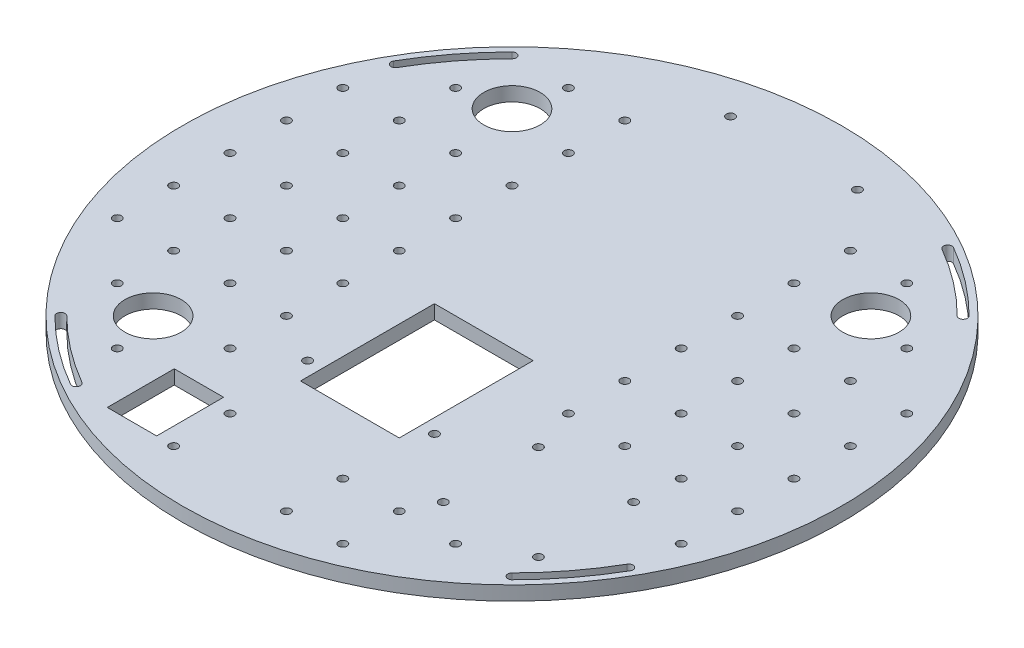
SolidWorks part; units mm, degrees
ref_plane "Front Plane" through (0, 0, 0) normal (0, 0, 1) x (1, 0, 0)
ref_plane "Top Plane" through (0, 0, 0) normal (0, 1, 0) x (1, 0, 0)
ref_plane "Right Plane" through (0, 0, 0) normal (1, 0, 0) x (0, 0, -1)
sketch "Sketch18" plane through (0, 0, 0) normal (0, 1, 0) x (1, 0, 0)
  circle A0 centre (0, 0) radius 148.4312
  dimension "D1" = 296.8625
extrude "Boss-Extrude1" add sketch "Sketch18" along normal blind 6.35
sketch "Sketch19" plane through (0, 6.35, 0) normal (0, 1, 0) x (1, 0, 0)
  line L0 (-71.842, -124.4341) -> (-124.4341, 71.842)
  line L1 (-101.6, -101.6) -> (101.6, -101.6)
  line L2 (-101.6, -101.6) -> (-101.6, 101.6)
  line L3 (-101.6, 101.6) -> (101.6, 101.6)
  line L4 (101.6, -101.6) -> (101.6, 101.6)
  line L5 (-101.6, -101.6) -> (101.6, 101.6) construction
  line L6 (-101.6, 101.6) -> (101.6, -101.6) construction
  line L7 (-71.842, -124.4341) -> (124.4341, -71.842)
  line L8 (124.4341, -71.842) -> (71.842, 124.4341)
  line L9 (-124.4341, 71.842) -> (71.842, 124.4341)
  line L18 (-86.7516, 29.347) -> (60.4555, 68.791)
  line L19 (-76.2, -50.8) -> (76.2, -50.8)
  line L20 (-76.2, -50.8) -> (-76.2, 50.8)
  line L21 (-76.2, 50.8) -> (76.2, 50.8)
  line L22 (76.2, -50.8) -> (76.2, 50.8)
  line L23 (-76.2, -50.8) -> (76.2, 50.8) construction
  line L24 (-76.2, 50.8) -> (76.2, -50.8) construction
  line L25 (-60.4555, -68.791) -> (-86.7516, 29.347)
  line L26 (-60.4555, -68.791) -> (86.7516, -29.347)
  line L27 (86.7516, -29.347) -> (60.4555, 68.791)
  circle A0 centre (0, 0) radius 143.6841
  point P0 (0, 0)
  dimension "D1" = 203.2
  dimension "D3" = 15
  dimension "D4" = 152.4
  dimension "D5" = 101.6
  dimension "D2" = 2
  dimension "D6" = 2
hole_wizard "#6 Clearance Hole1" positions "Sketch20" profile "Sketch21" hole size "#6" standard "ANSI Inch" end condition through all
sketch "Sketch20" plane through (0, 6.35, 0) normal (0, 1, 0) x (1, 0, 0)
  point P0 (-101.6, 101.6)
  point P3 (101.6, 101.6)
  point P6 (101.6, -101.6)
  point P9 (-101.6, -101.6)
  point P13 (-124.4341, 71.842)
  point P16 (-71.842, -124.4341)
  point P19 (124.4341, -71.842)
  point P22 (71.842, 124.4341)
  point P51 (0, 0)
  point P52 (0, 0)
  point P53 (0, 0)
sketch "Sketch21" plane through (-101.6, 6.35, -101.6) normal (1, 0, 0) x (0, 0, 1)
  line L0 (0, 0) -> (0, 6.35)
  line L1 (0, 6.35) -> (1.8986, 6.35)
  line L2 (1.8986, 6.35) -> (1.8986, 0)
  line L5 (1.8986, 0) -> (0, 0)
  line L11 (0, -6.35) -> (0, 107.95) construction
  dimension "Thru Hole Dia." = 3.7973
  dimension "Thru Hole Depth" = 6.35
sketch "Sketch23" plane through (0, 6.35, 0) normal (0, 1, 0) x (1, 0, 0)
  circle A0 centre (124.4341, -71.842) radius 1.8987 construction
  circle A1 centre (101.6, -101.6) radius 1.8986 construction
  circle A2 centre (-71.842, -124.4341) radius 1.8986 construction
  circle A3 centre (-101.6, -101.6) radius 1.8986 construction
  circle A4 centre (101.6, 101.6) radius 1.8986 construction
  circle A5 centre (71.842, 124.4341) radius 1.8986 construction
  circle A6 centre (-101.6, 101.6) radius 1.8986 construction
  circle A7 centre (-124.4341, 71.842) radius 1.8986 construction
  circle A8 centre (124.4341, -71.842) radius 1.8987
  circle A9 centre (101.6, -101.6) radius 1.8986
  circle A10 centre (-71.842, -124.4341) radius 1.8986
  circle A11 centre (-101.6, -101.6) radius 1.8986
  circle A12 centre (101.6, 101.6) radius 1.8986
  circle A13 centre (71.842, 124.4341) radius 1.8986
  circle A14 centre (-101.6, 101.6) radius 1.8986
  circle A15 centre (-124.4341, 71.842) radius 1.8986
  arc A16 (-124.4341, 71.842) -> (-101.6, 101.6) centre (0, 0) cw construction
  arc A17 (-102.9425, 102.9425) -> (-126.0784, 72.7914) centre (0, 0) ccw
  arc A18 (-100.2575, 100.2575) -> (-122.7898, 70.8927) centre (0, 0) ccw
  arc A19 (-100.2575, 100.2575) -> (-102.9425, 102.9425) centre (-101.6, 101.6) ccw
  arc A20 (-126.0784, 72.7914) -> (-122.7898, 70.8927) centre (-124.4341, 71.842) ccw
  arc A21 (71.842, 124.4341) -> (101.6, 101.6) centre (0, 0) cw construction
  arc A22 (102.9425, 102.9425) -> (72.7914, 126.0784) centre (0, 0) ccw
  arc A23 (100.2575, 100.2575) -> (70.8927, 122.7898) centre (0, 0) ccw
  arc A24 (100.2575, 100.2575) -> (102.9425, 102.9425) centre (101.6, 101.6) ccw
  arc A25 (72.7914, 126.0784) -> (70.8927, 122.7898) centre (71.842, 124.4341) ccw
  arc A26 (101.6, -101.6) -> (124.4341, -71.842) centre (0, 0) ccw construction
  arc A27 (102.9425, -102.9425) -> (126.0784, -72.7914) centre (0, 0) ccw
  arc A28 (100.2575, -100.2575) -> (122.7898, -70.8927) centre (0, 0) ccw
  arc A29 (100.2575, -100.2575) -> (102.9425, -102.9425) centre (101.6, -101.6) ccw
  arc A30 (126.0784, -72.7914) -> (122.7898, -70.8927) centre (124.4341, -71.842) ccw
  arc A31 (-101.6, -101.6) -> (-71.842, -124.4341) centre (0, 0) ccw construction
  arc A32 (-102.9425, -102.9425) -> (-72.7914, -126.0784) centre (0, 0) ccw
  arc A33 (-100.2575, -100.2575) -> (-70.8927, -122.7898) centre (0, 0) ccw
  arc A34 (-100.2575, -100.2575) -> (-102.9425, -102.9425) centre (-101.6, -101.6) ccw
  arc A35 (-72.7914, -126.0784) -> (-70.8927, -122.7898) centre (-71.842, -124.4341) ccw
  point P27 (-113.9923, 87.4693)
  point P35 (87.4693, 113.9923)
  point P43 (113.9923, -87.4693)
  point P50 (-87.4693, -113.9923)
  point P55 (0, 0)
  circle M9 centre (-124.4341, 71.842) radius 1.8986
  circle M10 centre (-71.842, -124.4341) radius 1.8986
  circle M11 centre (124.4341, -71.842) radius 1.8987
  circle M12 centre (71.842, 124.4341) radius 1.8986
extrude "Cut-Extrude1" cut sketch "Sketch23" against normal blind 6.35 contours A33 A11 A32 M10 | A18 A14 A17 M9 | A23 A12 A22 M12 | A28 A9 A27 M11
sketch "Sketch24" plane through (0, 6.35, 0) normal (0, 1, 0) x (1, 0, 0)
  line L1 (-28.575, -63.5) -> (28.575, -63.5)
  line L2 (-28.575, -63.5) -> (-28.575, 127)
  line L3 (-28.575, 127) -> (28.575, 127)
  line L4 (28.575, -63.5) -> (28.575, 127)
  line L5 (-28.575, -63.5) -> (28.575, 127) construction
  line L6 (-28.575, 127) -> (28.575, -63.5) construction
  line L7 (57.15, -88.1063) -> (100.0125, -88.1063)
  line L8 (57.15, -88.1063) -> (57.15, -45.2437)
  line L9 (57.15, -45.2437) -> (100.0125, -45.2437)
  line L10 (100.0125, -88.1063) -> (100.0125, -45.2437)
  line L11 (57.15, -88.1063) -> (100.0125, -45.2437) construction
  line L12 (57.15, -45.2437) -> (100.0125, -88.1063) construction
  circle A0 centre (0, 0) radius 148.4312 construction
  point P0 (0, 31.75)
  point P5 (81.9016, -82.55)
  point P6 (0, 0)
  point P10 (78.5813, -66.675)
  dimension "D1" = 190.5
  dimension "D2" = 57.15
  dimension "D3" = 127
  dimension "D4" = 42.8625
  dimension "D5" = 28.575
  dimension "D6" = 3.175
hole_wizard "#6 Clearance Hole2" positions "Sketch25" profile "Sketch26" hole size "#6" standard "ANSI Inch" end condition through all
sketch "Sketch25" plane through (0, 6.35, 0) normal (0, 1, 0) x (1, 0, 0)
  point P0 (57.15, -45.2437)
  point P3 (57.15, -88.1063)
  point P6 (100.0125, -88.1063)
  point P9 (100.0125, -45.2437)
  point P12 (-28.575, -63.5)
  point P15 (28.575, -63.5)
  point P18 (-28.575, 127)
  point P21 (28.575, 127)
sketch "Sketch26" plane through (57.15, 6.35, 45.2437) normal (1, 0, 0) x (0, 0, 1)
  line L0 (0, 0) -> (0, 6.35)
  line L1 (0, 6.35) -> (1.8986, 6.35)
  line L2 (1.8986, 6.35) -> (1.8986, 0)
  line L5 (1.8986, 0) -> (0, 0)
  line L11 (0, -6.35) -> (0, 107.95) construction
  dimension "Thru Hole Dia." = 3.7973
  dimension "Thru Hole Depth" = 6.35
sketch "Sketch29" plane through (0, 6.35, 0) normal (0, 1, 0) x (1, 0, 0)
  line L0 (-22.225, -73.025) -> (-22.225, -12.7)
  line L1 (-19.05, -69.85) -> (19.05, -69.85)
  line L2 (-19.05, -69.85) -> (-19.05, -15.875) construction
  line L3 (-19.05, -15.875) -> (19.05, -15.875)
  line L4 (19.05, -69.85) -> (19.05, -15.875)
  line L5 (-19.05, -69.85) -> (19.05, -15.875) construction
  line L6 (-19.05, -15.875) -> (19.05, -69.85) construction
  line L7 (-22.225, -12.7) -> (22.225, -12.7)
  line L8 (22.225, -73.025) -> (22.225, -12.7)
  line L9 (-22.225, -73.025) -> (22.225, -73.025)
  circle A1 centre (-28.575, -63.5) radius 1.8986 construction
  point P0 (0, -42.8625)
  point P5 (0, 94.9421)
  point P6 (0, 0)
  point P7 (0, -41.112)
  dimension "D3" = 6.35
  dimension "D1" = 38.1
  dimension "D2" = 53.975
  dimension "D4" = 3.175
extrude "Cut-Extrude2" cut sketch "Sketch29" against normal through all
sketch "Sketch30" plane through (0, 6.35, 0) normal (0, 1, 0) x (1, 0, 0)
  line L0 (-80.8223, 80.8223) -> (-80.8223, -80.8223) construction
  line L1 (-55.4223, -126.8598) -> (-33.1973, -126.8598)
  line L2 (-55.4223, -126.8598) -> (-55.4223, -96.6973)
  line L3 (-55.4223, -96.6973) -> (-33.1973, -96.6973)
  line L4 (-33.1973, -126.8598) -> (-33.1973, -96.6973)
  line L5 (-55.4223, -126.8598) -> (-33.1973, -96.6973) construction
  line L6 (-55.4223, -96.6973) -> (-33.1973, -126.8598) construction
  line L7 (-80.8223, 80.8223) -> (80.8223, 80.8223) construction
  circle A0 centre (-80.8223, 80.8223) radius 12.7
  circle A1 centre (80.8223, 80.8223) radius 12.7
  circle A2 centre (-80.8223, -80.8223) radius 12.7
  circle A3 centre (0, 0) radius 114.3 construction
  point P6 (-44.3098, -111.7786)
  point P14 (-130.789, 0)
  point P15 (0, 0)
  point P16 (0, 0)
  point P17 (-47.0634, -107.5133)
  dimension "D1" = 228.6
  dimension "D2" = 25.4
  dimension "D3" = 30.1625
  dimension "D4" = 22.225
  dimension "D5" = 25.4
  dimension "D6" = 15.875
extrude "Cut-Extrude3" cut sketch "Sketch30" against normal blind 6.35
sketch "Sketch31" plane through (0, 6.35, 0) normal (0, 1, 0) x (1, 0, 0)
  line L0 (-25.4, 0) -> (0, 0) construction
  line L1 (0, -148.4312) -> (0, 148.4312) construction
  circle A0 centre (0, 0) radius 148.4312 construction
  point P0 (-25.4, 0)
  point P3 (0, 0)
  point P5 (25.4, 127)
  point P6 (-50.8, 0)
  point P7 (-76.2, 0)
  point P8 (-101.6, 0)
  point P9 (-127, 0)
  point P10 (-50.8, 25.4)
  point P11 (-76.2, 25.4)
  point P12 (-101.6, 25.4)
  point P13 (-127, 25.4)
  point P14 (-50.8, 50.8)
  point P15 (-76.2, 50.8)
  point P16 (-101.6, 50.8)
  point P17 (-127, 50.8)
  point P18 (-50.8, 76.2)
  point P19 (-76.2, 76.2)
  point P20 (-101.6, 76.2)
  point P21 (-127, 76.2)
  point P22 (-50.8, 101.6)
  point P23 (-76.2, 101.6)
  point P24 (-101.6, 101.6)
  point P25 (-127, 101.6)
  point P26 (-50.8, 127)
  point P27 (-76.2, 127)
  point P28 (-101.6, 127)
  point P29 (-127, 127)
  point P30 (-25.4, 25.4)
  point P31 (-25.4, 50.8)
  point P32 (-25.4, 76.2)
  point P33 (-25.4, 101.6)
  point P34 (-25.4, 127)
  point P39 (25.4, 101.6)
  point P40 (25.4, 76.2)
  point P41 (25.4, 50.8)
  point P42 (25.4, 25.4)
  point P43 (127, 127)
  point P44 (101.6, 127)
  point P45 (76.2, 127)
  point P46 (50.8, 127)
  point P47 (127, 101.6)
  point P48 (101.6, 101.6)
  point P49 (76.2, 101.6)
  point P50 (50.8, 101.6)
  point P51 (127, 76.2)
  point P52 (101.6, 76.2)
  point P53 (76.2, 76.2)
  point P54 (50.8, 76.2)
  point P55 (127, 50.8)
  point P56 (101.6, 50.8)
  point P57 (76.2, 50.8)
  point P58 (50.8, 50.8)
  point P59 (127, 25.4)
  point P60 (101.6, 25.4)
  point P61 (76.2, 25.4)
  point P62 (50.8, 25.4)
  point P63 (127, 0)
  point P64 (101.6, 0)
  point P65 (76.2, 0)
  point P66 (50.8, 0)
  point P67 (25.4, 0)
  point P69 (50.8, -25.4)
  point P70 (76.2, -25.4)
  point P71 (101.6, -25.4)
  point P72 (127, -25.4)
  point P73 (50.8, -50.8)
  point P74 (76.2, -50.8)
  point P75 (101.6, -50.8)
  point P76 (127, -50.8)
  point P77 (50.8, -76.2)
  point P78 (76.2, -76.2)
  point P79 (101.6, -76.2)
  point P80 (127, -76.2)
  point P81 (50.8, -101.6)
  point P82 (76.2, -101.6)
  point P83 (101.6, -101.6)
  point P84 (127, -101.6)
  point P85 (50.8, -127)
  point P86 (76.2, -127)
  point P87 (101.6, -127)
  point P88 (127, -127)
  point P89 (25.4, -25.4)
  point P90 (25.4, -50.8)
  point P91 (25.4, -76.2)
  point P92 (25.4, -101.6)
  point P93 (-25.4, -127)
  point P94 (-25.4, -101.6)
  point P95 (-25.4, -76.2)
  point P96 (-25.4, -50.8)
  point P97 (-25.4, -25.4)
  point P98 (-127, -127)
  point P99 (-101.6, -127)
  point P100 (-76.2, -127)
  point P101 (-50.8, -127)
  point P102 (-127, -101.6)
  point P103 (-101.6, -101.6)
  point P104 (-76.2, -101.6)
  point P105 (-50.8, -101.6)
  point P106 (-127, -76.2)
  point P107 (-101.6, -76.2)
  point P108 (-76.2, -76.2)
  point P109 (-50.8, -76.2)
  point P110 (-127, -50.8)
  point P111 (-101.6, -50.8)
  point P112 (-76.2, -50.8)
  point P113 (-50.8, -50.8)
  point P114 (-127, -25.4)
  point P115 (-101.6, -25.4)
  point P116 (-76.2, -25.4)
  point P117 (-50.8, -25.4)
  point P118 (25.4, -127)
  dimension "D1" = 25.4
  dimension "D2" = 5
  dimension "D3" = 6
hole_wizard "#6 Clearance Hole3" positions "Sketch32" profile "Sketch33" hole size "#6" standard "ANSI Inch" end condition through all
sketch "Sketch32" plane through (0, 6.35, 0) normal (0, 1, 0) x (1, 0, 0)
  point P0 (-50.8, 101.6)
  point P3 (-76.2, 101.6)
  point P6 (-101.6, 76.2)
  point P9 (-50.8, 76.2)
  point P12 (-50.8, 50.8)
  point P15 (-76.2, 50.8)
  point P18 (-101.6, 50.8)
  point P21 (-127, 50.8)
  point P24 (-50.8, 25.4)
  point P27 (-76.2, 25.4)
  point P30 (-101.6, 25.4)
  point P33 (-127, 25.4)
  point P36 (-101.6, 0)
  point P39 (-127, 0)
  point P42 (-127, -25.4)
  point P45 (-101.6, -25.4)
  point P48 (-127, -50.8)
  point P51 (-101.6, -50.8)
  point P54 (-101.6, -76.2)
  point P57 (-76.2, -101.6)
  point P60 (-50.8, -76.2)
  point P63 (-76.2, -50.8)
  point P66 (-50.8, -50.8)
  point P69 (-50.8, -25.4)
  point P72 (-76.2, -25.4)
  point P75 (-76.2, 0)
  point P78 (-50.8, 0)
  point P81 (50.8, 101.6)
  point P84 (76.2, 101.6)
  point P87 (50.8, 76.2)
  point P90 (101.6, 76.2)
  point P93 (101.6, 50.8)
  point P96 (127, 50.8)
  point P99 (127, 25.4)
  point P102 (127, 0)
  point P105 (127, -25.4)
  point P108 (50.8, 50.8)
  point P111 (50.8, 25.4)
  point P114 (50.8, 0)
  point P117 (50.8, -25.4)
  point P120 (76.2, -25.4)
  point P123 (101.6, -25.4)
  point P126 (101.6, 0)
  point P129 (76.2, 0)
  point P132 (76.2, 25.4)
  point P135 (76.2, 50.8)
  point P138 (101.6, 25.4)
  point P141 (127, -50.8)
  point P144 (76.2, -101.6)
  point P147 (50.8, -101.6)
  point P150 (-25.4, -101.6)
  point P153 (25.4, -101.6)
  point P156 (25.4, -127)
  point P159 (50.8, -127)
  point P162 (-25.4, -127)
sketch "Sketch33" plane through (-50.8, 6.35, -101.6) normal (1, 0, 0) x (0, 0, 1)
  line L0 (0, 0) -> (0, 6.35)
  line L1 (0, 6.35) -> (1.8986, 6.35)
  line L2 (1.8986, 6.35) -> (1.8986, 0)
  line L5 (1.8986, 0) -> (0, 0)
  line L11 (0, -6.35) -> (0, 107.95) construction
  dimension "Thru Hole Dia." = 3.7973
  dimension "Thru Hole Depth" = 6.35
